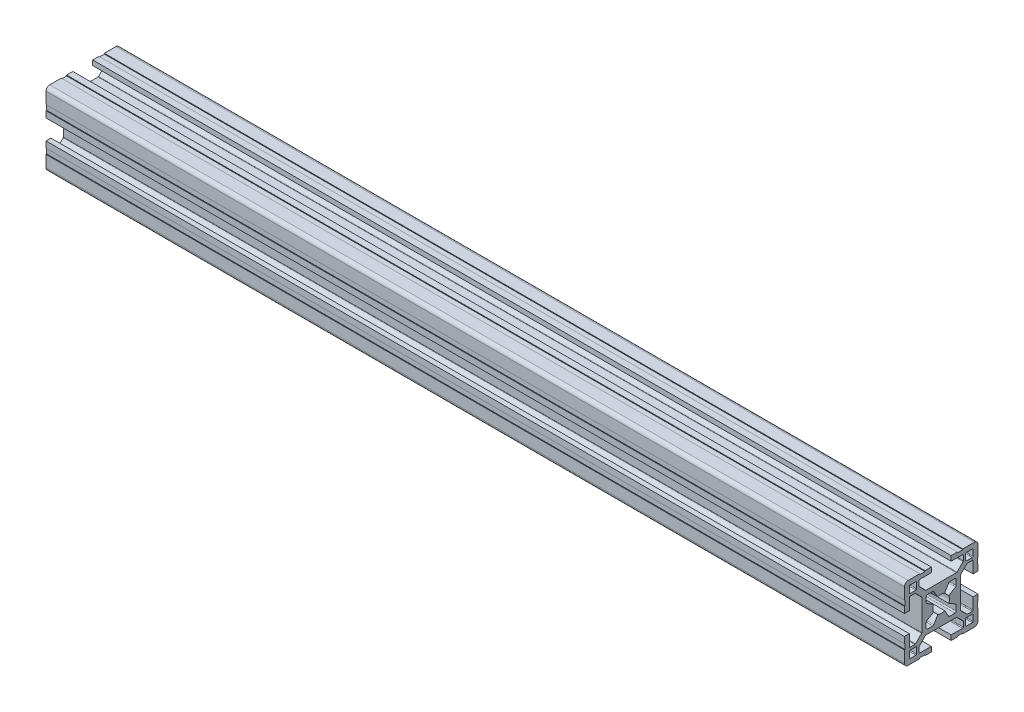
SolidWorks part; units mm, degrees
material "6063-T5"
ref_plane "Plano frontal" through (0, 0, 0) normal (0, 0, 1) x (1, 0, 0)
ref_plane "Plano superior" through (0, 0, 0) normal (0, 1, 0) x (1, 0, 0)
ref_plane "Plano direito" through (0, 0, 0) normal (1, 0, 0) x (0, 0, -1)
sketch "Esboço1" plane through (0, 0, 0) normal (0, 0, 1) x (1, 0, 0)
  line L0 (0, 0) -> (350, 0)
  point P3 (175, 0)
  dimension "D1" = 350
other "Quadrado PF30-11 - PERFIL 3030 CENTRO M8(1)"
ref_plane "Plano1" through (0, 0, 0) normal (1, 0, 0) x (0, 1, 0)
sketch "Sketch1" plane through (0, 0, 0) normal (1, 0, 0) x (0, 1, 0)
  line L0 (-6.1, -3.4254) -> (-6.1, -5.6)
  line L1 (-5.6, -6.1) -> (-3.4254, -6.1)
  line L2 (3.4254, -6.1) -> (5.6, -6.1)
  line L3 (6.1, -5.6) -> (6.1, -3.4254)
  line L4 (6.1, 3.4254) -> (6.1, 5.6)
  line L5 (5.6, 6.1) -> (3.4254, 6.1)
  line L6 (-3.4254, 6.1) -> (-5.6, 6.1)
  line L7 (-6.1, 5.6) -> (-6.1, 3.4254)
  line L8 (15, 6.6) -> (14.7, 6.6)
  line L9 (5.85, -2.9924) -> (3.097, -1.403)
  line L10 (10, 12.7) -> (10, 10.3)
  line L11 (13, -12.7) -> (13, -10.3)
  line L12 (-10.3, -10) -> (-12.7, -10)
  line L13 (-13, 12.7) -> (-13, 10.3)
  line L14 (3.097, 1.403) -> (5.85, 2.9924)
  line L15 (2.9924, 5.85) -> (1.403, 3.097)
  line L16 (-1.403, 3.097) -> (-2.9924, 5.85)
  line L17 (-5.85, 2.9924) -> (-3.097, 1.403)
  line L18 (-3.097, -1.403) -> (-5.85, -2.9924)
  line L19 (-2.9924, -5.85) -> (-1.403, -3.097)
  line L20 (1.403, -3.097) -> (2.9924, -5.85)
  line L21 (10.3, 10) -> (12.7, 10)
  line L22 (13, 10.3) -> (13, 12.7)
  line L23 (12.7, 13) -> (10.3, 13)
  line L24 (12.7, -10) -> (10.3, -10)
  line L25 (10, -10.3) -> (10, -12.7)
  line L26 (10.3, -13) -> (12.7, -13)
  line L27 (-13, -10.3) -> (-13, -12.7)
  line L28 (-12.7, -13) -> (-10.3, -13)
  line L29 (-10, -12.7) -> (-10, -10.3)
  line L30 (-12.7, 10) -> (-10.3, 10)
  line L31 (-10, 10.3) -> (-10, 12.7)
  line L32 (-10.3, 13) -> (-12.7, 13)
  line L33 (15, 4.05) -> (15, 6.6)
  line L34 (13, 4.05) -> (15, 4.05)
  line L35 (13, 8.7) -> (13, 4.05)
  line L36 (10.6799, 9) -> (12.7, 9)
  line L37 (7.9879, 6.4322) -> (10.4678, 8.9121)
  line L38 (7.9, -6.2201) -> (7.9, 6.2201)
  line L39 (10.4678, -8.9121) -> (7.9879, -6.4322)
  line L40 (12.7, -9) -> (10.6799, -9)
  line L41 (13, -4.05) -> (13, -8.7)
  line L42 (15, -4.05) -> (13, -4.05)
  line L43 (15, -6.6) -> (15, -4.05)
  line L44 (14.7, -6.6) -> (15, -6.6)
  line L45 (14.7, -8.8) -> (14.7, -6.6)
  line L46 (15, -8.8) -> (14.7, -8.8)
  line L47 (15, -13.5) -> (15, -8.8)
  line L48 (8.8, -15) -> (13.5, -15)
  line L49 (8.8, -14.7) -> (8.8, -15)
  line L50 (6.6, -14.7) -> (8.8, -14.7)
  line L51 (6.6, -15) -> (6.6, -14.7)
  line L52 (4.05, -15) -> (6.6, -15)
  line L53 (4.05, -13) -> (4.05, -15)
  line L54 (8.7, -13) -> (4.05, -13)
  line L55 (9, -10.6799) -> (9, -12.7)
  line L56 (6.4322, -7.9879) -> (8.9121, -10.4678)
  line L57 (-6.2201, -7.9) -> (6.2201, -7.9)
  line L58 (-8.9121, -10.4678) -> (-6.4322, -7.9879)
  line L59 (-9, -12.7) -> (-9, -10.6799)
  line L60 (-4.05, -13) -> (-8.7, -13)
  line L61 (-4.05, -15) -> (-4.05, -13)
  line L62 (-6.6, -15) -> (-4.05, -15)
  line L63 (-6.6, -14.7) -> (-6.6, -15)
  line L64 (-8.8, -14.7) -> (-6.6, -14.7)
  line L65 (-8.8, -15) -> (-8.8, -14.7)
  line L66 (-13.5, -15) -> (-8.8, -15)
  line L67 (-15, -8.8) -> (-15, -13.5)
  line L68 (-14.7, -8.8) -> (-15, -8.8)
  line L69 (-14.7, -6.6) -> (-14.7, -8.8)
  line L70 (-15, -6.6) -> (-14.7, -6.6)
  line L71 (-15, -4.05) -> (-15, -6.6)
  line L72 (-13, -4.05) -> (-15, -4.05)
  line L73 (-13, -8.7) -> (-13, -4.05)
  line L74 (-10.6799, -9) -> (-12.7, -9)
  line L75 (-7.9879, -6.4322) -> (-10.4678, -8.9121)
  line L76 (-7.9, 6.2201) -> (-7.9, -6.2201)
  line L77 (-10.4678, 8.9121) -> (-7.9879, 6.4322)
  line L78 (-12.7, 9) -> (-10.6799, 9)
  line L79 (-13, 4.05) -> (-13, 8.7)
  line L80 (-15, 4.05) -> (-13, 4.05)
  line L81 (-15, 6.6) -> (-15, 4.05)
  line L82 (-14.7, 6.6) -> (-15, 6.6)
  line L83 (-14.7, 8.8) -> (-14.7, 6.6)
  line L84 (-15, 8.8) -> (-14.7, 8.8)
  line L85 (-15, 13.5) -> (-15, 8.8)
  line L86 (-8.8, 15) -> (-13.5, 15)
  line L87 (-8.8, 14.7) -> (-8.8, 15)
  line L88 (-6.6, 14.7) -> (-8.8, 14.7)
  line L89 (-6.6, 15) -> (-6.6, 14.7)
  line L90 (-4.05, 15) -> (-6.6, 15)
  line L91 (-4.05, 13) -> (-4.05, 15)
  line L92 (-8.7, 13) -> (-4.05, 13)
  line L93 (-9, 10.6799) -> (-9, 12.7)
  line L94 (-6.4322, 7.9879) -> (-8.9121, 10.4678)
  line L95 (6.2201, 7.9) -> (-6.2201, 7.9)
  line L96 (8.9121, 10.4678) -> (6.4322, 7.9879)
  line L97 (9, 12.7) -> (9, 10.6799)
  line L98 (4.05, 13) -> (8.7, 13)
  line L99 (4.05, 15) -> (4.05, 13)
  line L100 (6.6, 15) -> (4.05, 15)
  line L101 (6.6, 14.7) -> (6.6, 15)
  line L102 (8.8, 14.7) -> (6.6, 14.7)
  line L103 (8.8, 15) -> (8.8, 14.7)
  line L104 (13.5, 15) -> (8.8, 15)
  line L105 (15, 8.8) -> (15, 13.5)
  line L106 (14.7, 8.8) -> (15, 8.8)
  line L107 (14.7, 6.6) -> (14.7, 8.8)
  arc A0 (-5.85, -2.9924) -> (-6.1, -3.4254) centre (-5.6, -3.4254) ccw
  arc A1 (-6.1, -5.6) -> (-5.6, -6.1) centre (-5.6, -5.6) ccw
  arc A2 (-3.4254, -6.1) -> (-2.9924, -5.85) centre (-3.4254, -5.6) ccw
  arc A3 (2.9924, -5.85) -> (3.4254, -6.1) centre (3.4254, -5.6) ccw
  arc A4 (5.6, -6.1) -> (6.1, -5.6) centre (5.6, -5.6) ccw
  arc A5 (6.1, -3.4254) -> (5.85, -2.9924) centre (5.6, -3.4254) ccw
  arc A6 (5.85, 2.9924) -> (6.1, 3.4254) centre (5.6, 3.4254) ccw
  arc A7 (6.1, 5.6) -> (5.6, 6.1) centre (5.6, 5.6) ccw
  arc A8 (3.4254, 6.1) -> (2.9924, 5.85) centre (3.4254, 5.6) ccw
  arc A9 (-2.9924, 5.85) -> (-3.4254, 6.1) centre (-3.4254, 5.6) ccw
  arc A10 (-5.6, 6.1) -> (-6.1, 5.6) centre (-5.6, 5.6) ccw
  arc A11 (-6.1, 3.4254) -> (-5.85, 2.9924) centre (-5.6, 3.4254) ccw
  arc A12 (3.097, -1.403) -> (3.097, 1.403) centre (0, 0) ccw
  arc A13 (1.403, 3.097) -> (-1.403, 3.097) centre (0, 0) ccw
  arc A14 (-3.097, 1.403) -> (-3.097, -1.403) centre (0, 0) ccw
  arc A15 (-1.403, -3.097) -> (1.403, -3.097) centre (0, 0) ccw
  arc A16 (10, 10.3) -> (10.3, 10) centre (10.3, 10.3) ccw
  arc A17 (12.7, 10) -> (13, 10.3) centre (12.7, 10.3) ccw
  arc A18 (13, 12.7) -> (12.7, 13) centre (12.7, 12.7) ccw
  arc A19 (10.3, 13) -> (10, 12.7) centre (10.3, 12.7) ccw
  arc A20 (13, -10.3) -> (12.7, -10) centre (12.7, -10.3) ccw
  arc A21 (10.3, -10) -> (10, -10.3) centre (10.3, -10.3) ccw
  arc A22 (10, -12.7) -> (10.3, -13) centre (10.3, -12.7) ccw
  arc A23 (12.7, -13) -> (13, -12.7) centre (12.7, -12.7) ccw
  arc A24 (-12.7, -10) -> (-13, -10.3) centre (-12.7, -10.3) ccw
  arc A25 (-13, -12.7) -> (-12.7, -13) centre (-12.7, -12.7) ccw
  arc A26 (-10.3, -13) -> (-10, -12.7) centre (-10.3, -12.7) ccw
  arc A27 (-10, -10.3) -> (-10.3, -10) centre (-10.3, -10.3) ccw
  arc A28 (-13, 10.3) -> (-12.7, 10) centre (-12.7, 10.3) ccw
  arc A29 (-10.3, 10) -> (-10, 10.3) centre (-10.3, 10.3) ccw
  arc A30 (-10, 12.7) -> (-10.3, 13) centre (-10.3, 12.7) ccw
  arc A31 (-12.7, 13) -> (-13, 12.7) centre (-12.7, 12.7) ccw
  arc A32 (13, 8.7) -> (12.7, 9) centre (12.7, 8.7) ccw
  arc A33 (10.6799, 9) -> (10.4678, 8.9121) centre (10.6799, 8.7) ccw
  arc A34 (7.9879, 6.4322) -> (7.9, 6.2201) centre (8.2, 6.2201) ccw
  arc A35 (7.9, -6.2201) -> (7.9879, -6.4322) centre (8.2, -6.2201) ccw
  arc A36 (10.4678, -8.9121) -> (10.6799, -9) centre (10.6799, -8.7) ccw
  arc A37 (12.7, -9) -> (13, -8.7) centre (12.7, -8.7) ccw
  arc A38 (13.5, -15) -> (15, -13.5) centre (13.5, -13.5) ccw
  arc A39 (8.7, -13) -> (9, -12.7) centre (8.7, -12.7) ccw
  arc A40 (9, -10.6799) -> (8.9121, -10.4678) centre (8.7, -10.6799) ccw
  arc A41 (6.4322, -7.9879) -> (6.2201, -7.9) centre (6.2201, -8.2) ccw
  arc A42 (-6.2201, -7.9) -> (-6.4322, -7.9879) centre (-6.2201, -8.2) ccw
  arc A43 (-8.9121, -10.4678) -> (-9, -10.6799) centre (-8.7, -10.6799) ccw
  arc A44 (-9, -12.7) -> (-8.7, -13) centre (-8.7, -12.7) ccw
  arc A45 (-15, -13.5) -> (-13.5, -15) centre (-13.5, -13.5) ccw
  arc A46 (-13, -8.7) -> (-12.7, -9) centre (-12.7, -8.7) ccw
  arc A47 (-10.6799, -9) -> (-10.4678, -8.9121) centre (-10.6799, -8.7) ccw
  arc A48 (-7.9879, -6.4322) -> (-7.9, -6.2201) centre (-8.2, -6.2201) ccw
  arc A49 (-7.9, 6.2201) -> (-7.9879, 6.4322) centre (-8.2, 6.2201) ccw
  arc A50 (-10.4678, 8.9121) -> (-10.6799, 9) centre (-10.6799, 8.7) ccw
  arc A51 (-12.7, 9) -> (-13, 8.7) centre (-12.7, 8.7) ccw
  arc A52 (-13.5, 15) -> (-15, 13.5) centre (-13.5, 13.5) ccw
  arc A53 (-8.7, 13) -> (-9, 12.7) centre (-8.7, 12.7) ccw
  arc A54 (-9, 10.6799) -> (-8.9121, 10.4678) centre (-8.7, 10.6799) ccw
  arc A55 (-6.4322, 7.9879) -> (-6.2201, 7.9) centre (-6.2201, 8.2) ccw
  arc A56 (6.2201, 7.9) -> (6.4322, 7.9879) centre (6.2201, 8.2) ccw
  arc A57 (8.9121, 10.4678) -> (9, 10.6799) centre (8.7, 10.6799) ccw
  arc A58 (9, 12.7) -> (8.7, 13) centre (8.7, 12.7) ccw
  arc A59 (15, 13.5) -> (13.5, 15) centre (13.5, 13.5) ccw
  point P1 (0, 0)
  point P2 (0, 0)
  point P3 (-15, -15)
  point P4 (0, -15)
  point P5 (-15, 0)
  point P230 (-15, 15)
  point P231 (0, 15)
  point P232 (15, 15)
  point P233 (15, 0)
  point P234 (15, -15)
  point P235 (0, -15)
  point P236 (-15, -15)
  point P237 (-15, 0)
  point P238 (0, 0)
  point P239 (0, 0)
